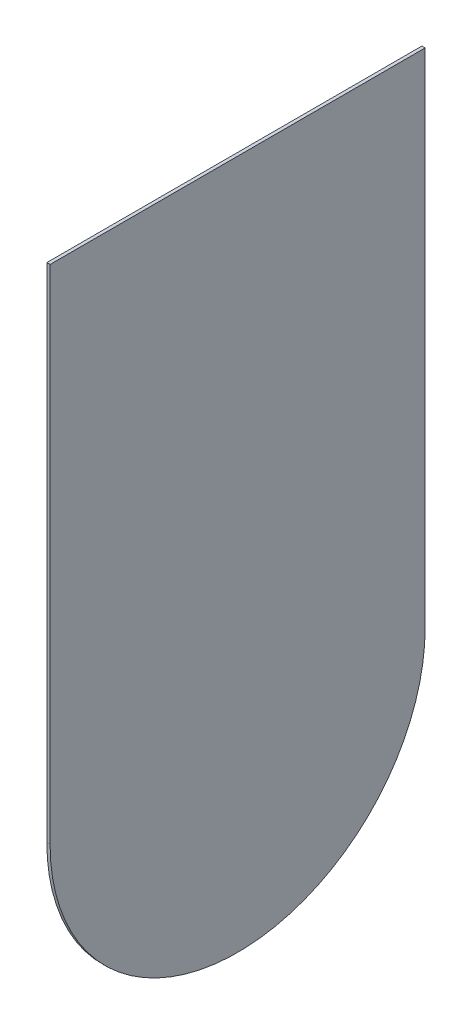
SolidWorks part; units mm, degrees
ref_plane "Front Plane" through (0, 0, 0) normal (0, 0, 1) x (1, 0, 0)
ref_plane "Top Plane" through (0, 0, 0) normal (0, 1, 0) x (1, 0, 0)
ref_plane "Right Plane" through (0, 0, 0) normal (1, 0, 0) x (0, 0, -1)
sketch "Sketch1" plane through (0, 0, 0) normal (1, 0, 0) x (0, 0, -1)
  line L1 (-13.3165, 21.0534) -> (12.0835, 21.0534)
  line L2 (-13.3165, 21.0534) -> (-13.3165, -12.9466)
  line L3 (-13.3165, -12.9466) -> (12.0835, -12.9466)
  line L4 (12.0835, 21.0534) -> (12.0835, -12.9466)
  arc A0 (-13.3165, -12.9466) -> (12.0835, -12.9466) centre (-0.6165, -12.9466) ccw
  dimension "D1" = 25.4
  dimension "D2" = 34
extrude "Boss-Extrude1" add sketch "Sketch1" along normal blind 0.22 contours L3 A0 | L4 L1 L2 L3
